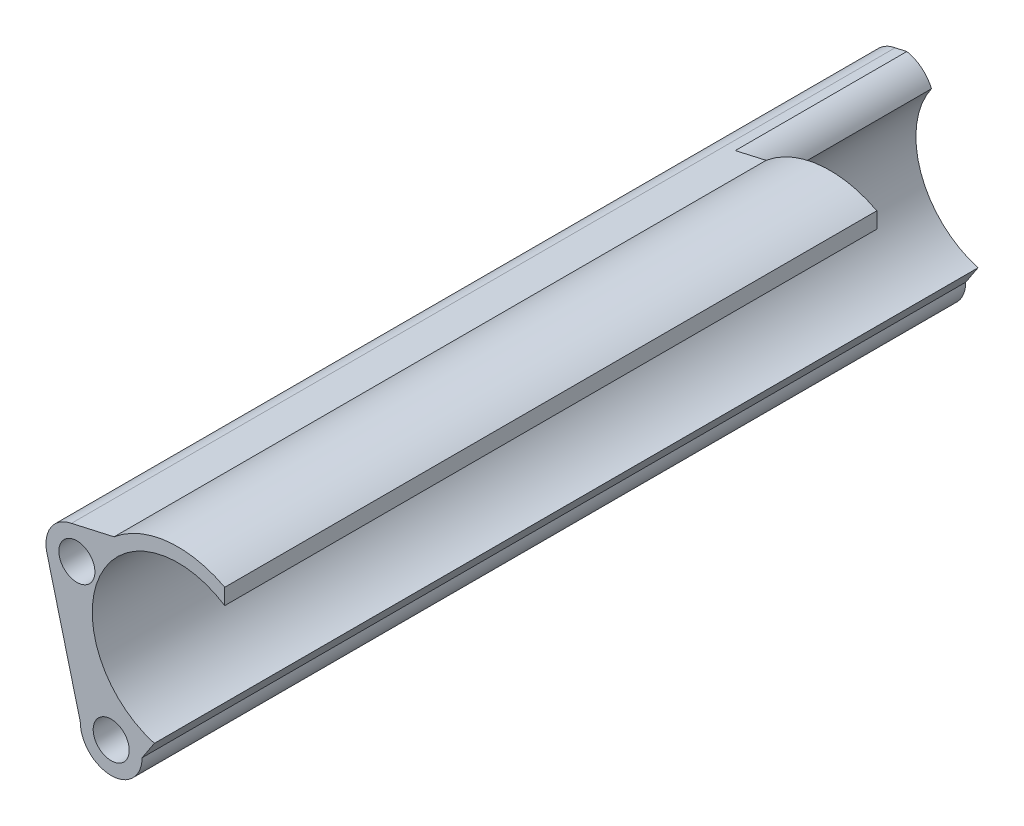
SolidWorks part; units mm, degrees
ref_plane "Plan de face" through (0, 0, 0) normal (0, 0, 1) x (1, 0, 0)
ref_plane "Plan de dessus" through (0, 0, 0) normal (0, 1, 0) x (1, 0, 0)
ref_plane "Plan de droite" through (0, 0, 0) normal (1, 0, 0) x (0, 0, -1)
sketch "Esquisse1" plane through (0, 0, 0) normal (0, 0, 1) x (1, 0, 0)
  line L0 (-4.358, -1.1215) -> (0.5, -20)
  line L8 (5.4196, 5.8362) -> (-0.7976, 4.4288)
  line L9 (10.5992, -17.0688) -> (11.5992, -16.8114)
  line L10 (11.5992, -16.8114) -> (9.5, -20)
  line L12 (21.5407, 7.5313) -> (21.5407, 5.2128)
  circle A0 centre (0, 0) radius 2.625
  circle A1 centre (5, -20) radius 2.625
  arc A3 (0.5, -20) -> (9.5, -20) centre (5, -20) ccw
  arc A4 (-0.7976, 4.4288) -> (-4.358, -1.1215) centre (0, 0) ccw
  arc A5 (10.3767, 6.4411) -> (10.5992, -17.0688) centre (14.7374, -5.2736) ccw
  arc A6 (21.5407, 5.2128) -> (11.2857, -17.2876) centre (14.7374, -5.2736) ccw
  arc A7 (21.5407, 7.5313) -> (5.4196, 5.8362) centre (14.7374, -5.2736) ccw
  point P13 (21.5407, 9.2264)
  point P14 (0, 0)
  dimension "D1" = 5.25
  dimension "D2" = 5.25
  dimension "D5" = 25
  dimension "D6" = 9
  dimension "D10" = 29
  dimension "D3" = 5
  dimension "D4" = 20
  dimension "D7" = 5.5992
  dimension "D8" = 2.9312
  dimension "D9" = 1
extrude "Boss.-Extru.1" add sketch "Esquisse1" along normal blind 120
sketch "Esquisse2" plane through (0, 0, 0) normal (0, 0, -1) x (-1, 0, 0)
  line L0 (-0.8026, 4.8385) -> (-23.5422, 15.3334)
  line L1 (-23.5422, 15.3334) -> (-23.5422, 4.1407)
  line L2 (-23.5422, 4.1407) -> (-4.5138, 1.9186)
  arc A0 (-0.8026, 4.8385) -> (-4.5138, 1.9186) centre (0, 0) ccw
  arc A1 (-11.2857, -17.2876) -> (-21.5407, 5.2128) centre (-14.7374, -5.2736) ccw construction
  point P1 (-15.084, 9.351)
  point P7 (-15.5269, 7.0627)
  point P11 (0, 0)
  point P12 (0, 0)
  point P16 (-15.8535, 11.7849)
  point P17 (-23.5422, 4.1407)
extrude "Enlèv. mat.-Extru.1" cut sketch "Esquisse2" against normal blind 25
